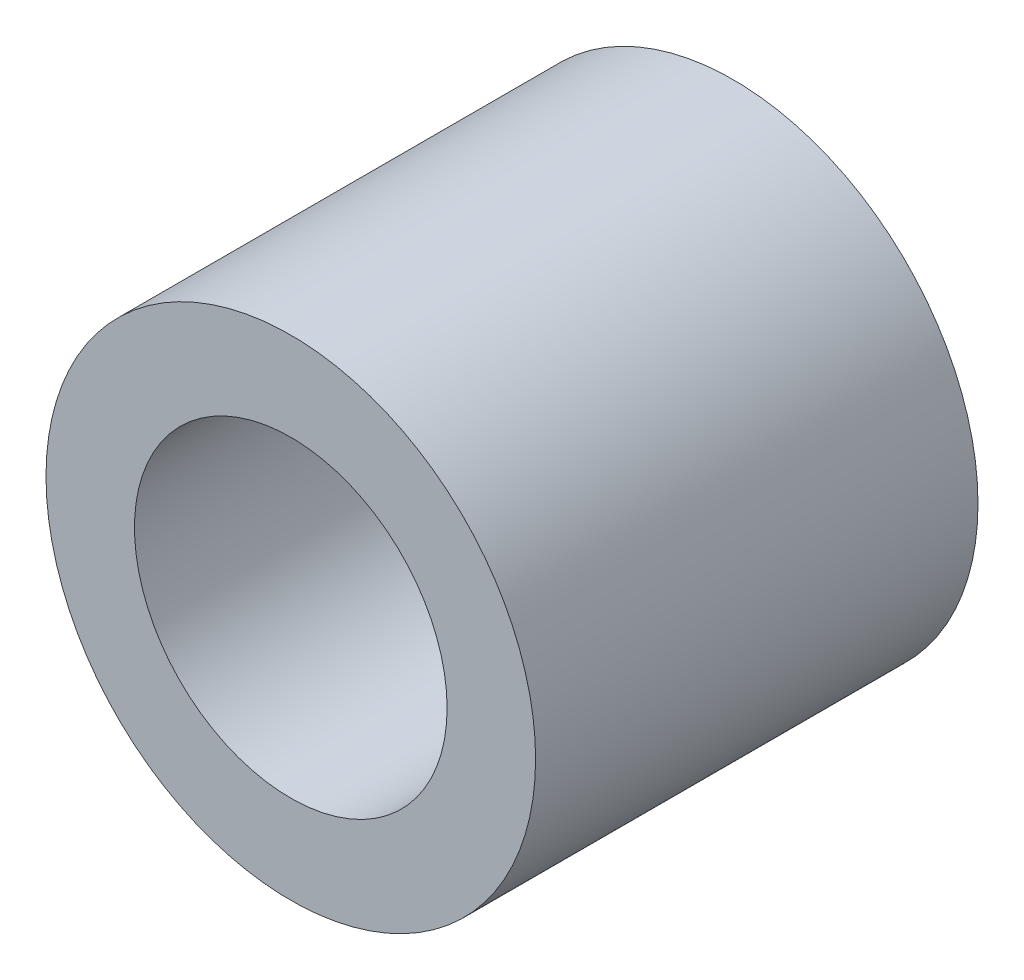
SolidWorks part; units mm, degrees
ref_plane "Front Plane" through (0, 0, 0) normal (0, 0, 1) x (1, 0, 0)
ref_plane "Top Plane" through (0, 0, 0) normal (0, 1, 0) x (1, 0, 0)
ref_plane "Right Plane" through (0, 0, 0) normal (1, 0, 0) x (0, 0, -1)
sketch "Sketch1" plane through (0, 0, 0) normal (0, 0, 1) x (1, 0, 0)
  circle A0 centre (0, 0) radius 2.65
  circle A1 centre (0, 0) radius 4.15
  dimension "D1" = 5.3
  dimension "D2" = 8.3
extrude "Boss-Extrude1" add sketch "Sketch1" along normal blind 7.5
